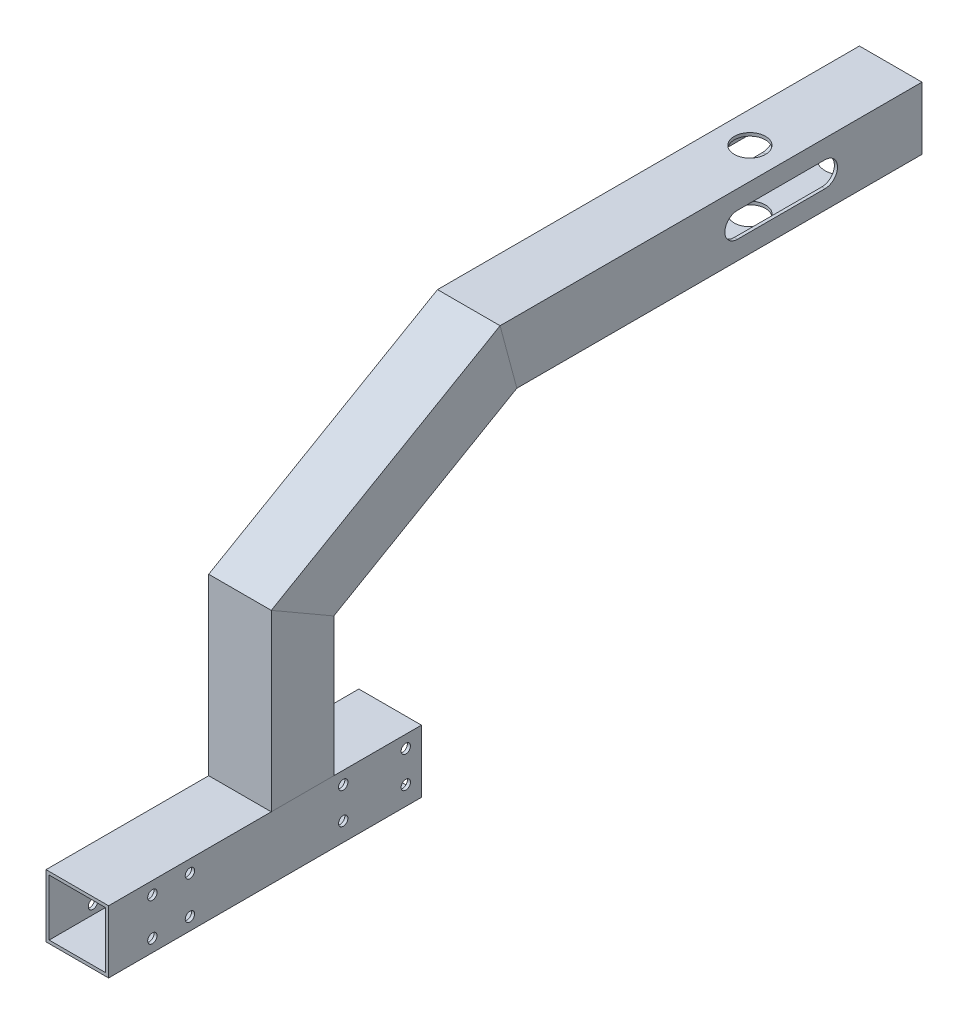
SolidWorks part; units mm, degrees
material "6063-O"
ref_plane "Front" through (0, 0, 0) normal (0, 0, 1) x (1, 0, 0)
ref_plane "Top" through (0, 0, 0) normal (0, 1, 0) x (1, 0, 0)
ref_plane "Right" through (0, 0, 0) normal (1, 0, 0) x (0, 0, -1)
sketch "草图1" plane through (0, 0, 0) normal (1, 0, 0) x (0, 0, -1)
  line L0 (0, 0) -> (62, 0) construction
  line L1 (62, 0) -> (62, 98) construction
  line L2 (62, 98) -> (260, 98) construction
  line L3 (0, 0) -> (100, 0)
  line L4 (62, 0) -> (62, 60)
  line L5 (62, 60) -> (127.8179, 98)
  line L6 (127.8179, 98) -> (260, 98)
  dimension "D1" = 62
  dimension "D2" = 98
  dimension "D3" = 198
  dimension "D4" = 100
  dimension "D5" = 60
  dimension "D6" = 60
other "铝管 20X20X1(14)"
ref_plane "基准面1" through (0, 0, 0) normal (0, 0, -1) x (0, 1, 0)
sketch "草图11" plane through (0, 0, 0) normal (0, 0, -1) x (0, 1, 0)
  line L1 (-10, -10) -> (10, -10)
  line L2 (-10, -10) -> (-10, 10)
  line L3 (-10, 10) -> (10, 10)
  line L4 (10, -10) -> (10, 10)
  line L5 (-10, -10) -> (10, 10) construction
  line L6 (-10, 10) -> (10, -10) construction
  line L7 (-9, -9) -> (9, -9)
  line L8 (-9, -9) -> (-9, 9)
  line L9 (-9, 9) -> (9, 9)
  line L10 (9, -9) -> (9, 9)
  line L11 (-9, -9) -> (9, 9) construction
  line L12 (-9, 9) -> (9, -9) construction
  point P0 (0, 0)
  point P6 (0, 0)
  point P11 (0, 0)
  dimension "D1" = 20
  dimension "D2" = 20
  dimension "D3" = 18
  dimension "D4" = 18
sketch "草图12" plane through (10, 0, 0) normal (1, 0, 0) x (0, 0, -1)
  line L0 (0, 0) -> (100, 0) construction
  line L1 (0, 10) -> (0, -10) construction
  line L2 (100, 10) -> (100, -10) construction
  circle A0 centre (14, 6) radius 1.5
  circle A1 centre (14, -6) radius 1.5
  circle A2 centre (26, 6) radius 1.5
  circle A3 centre (26, -6) radius 1.5
  dimension "D1" = 3
  dimension "D2" = 3
  dimension "D3" = 12
  dimension "D4" = 14
  dimension "D5" = 2
extrude "切除-拉伸1" cut sketch "草图12" against normal through all
sketch "草图13" plane through (0, 88, 0) normal (0, -1, 0) x (1, 0, 0)
  line L0 (0, 0) -> (0, -260) construction
  line L1 (10, 0) -> (-10, 0) construction
  line L2 (10, -260) -> (-10, -260) construction
  circle A0 centre (0, -215) radius 5
  dimension "D1" = 10
  dimension "D2" = 215
extrude "切除-拉伸2" cut sketch "草图13" against normal through all
sketch "草图14" plane through (10, 0, 0) normal (1, 0, 0) x (0, 0, -1)
  line L0 (201, 98) -> (229, 98) construction
  line L1 (201, 102) -> (229, 102)
  line L2 (201, 94) -> (229, 94)
  line L3 (0, 10) -> (0, -10) construction
  line L4 (260, 108) -> (125.1384, 108) construction
  arc A0 (201, 102) -> (201, 94) centre (201, 98) ccw
  arc A1 (229, 94) -> (229, 102) centre (229, 98) ccw
  point P2 (215, 98)
  dimension "D4" = 28
  dimension "D1" = 215
  dimension "D2" = 10
  dimension "D3" = 8
extrude "切除-拉伸3" cut sketch "草图14" against normal through all
sketch "草图15" plane through (0, 88, 0) normal (0, -1, 0) x (1, 0, 0)
  line L0 (0, -260) -> (0, -226.8111) construction
  line L1 (10, -260) -> (-10, -260) construction
  circle A0 centre (0, -245) radius 6
  dimension "D1" = 12
  dimension "D2" = 15
extrude "切除-拉伸4" cut sketch "草图15" against normal up to next (1 mm away)
sketch "草图16" plane through (0, 88, 0) normal (0, -1, 0) x (1, 0, 0)
  line L0 (10, -260) -> (-10, -260) construction
  line L1 (10, -260) -> (10, -130.4974) construction
  circle A0 centre (6, -254) radius 1.5
  dimension "D1" = 3
  dimension "D2" = 6
  dimension "D3" = 4
extrude "切除-拉伸5" cut sketch "草图16" against normal up to next (1 mm away)
sketch "草图17" plane through (10, 0, 0) normal (1, 0, 0) x (0, 0, -1)
  circle A0 centre (95, -4) radius 1.5
  circle A1 centre (95, 6) radius 1.5
  circle A2 centre (75, 6) radius 1.5
  circle A3 centre (75, -4) radius 1.5
extrude "切除-拉伸6" cut sketch "草图17" against normal blind 20
